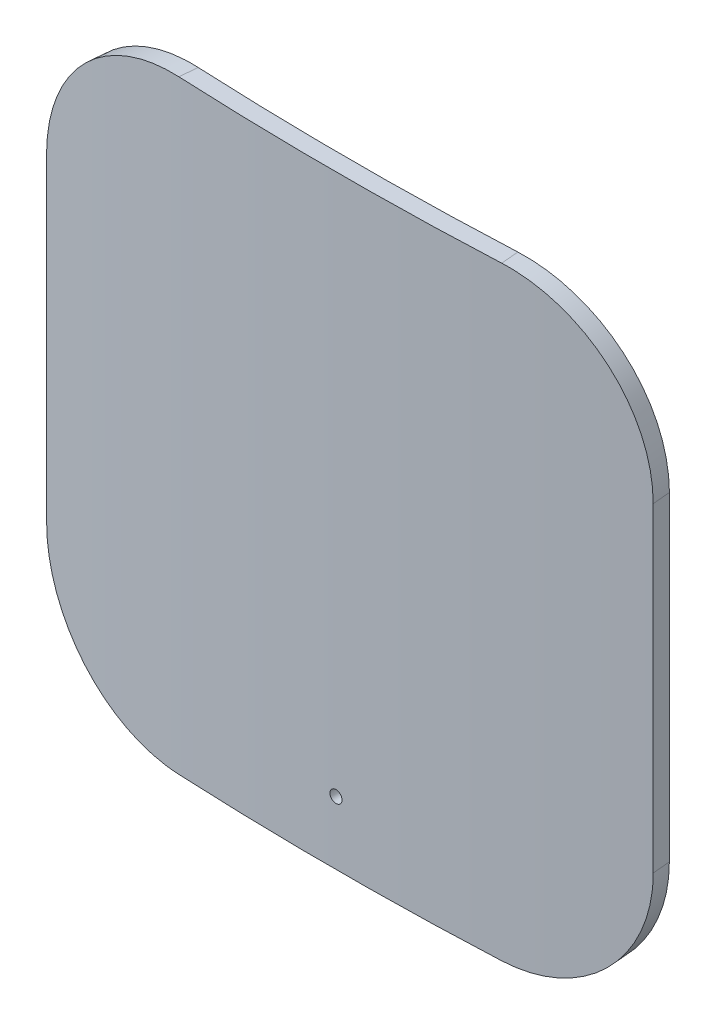
SolidWorks part; units mm, degrees
material "S235JR"
ref_plane "Ebene vorne" through (0, 0, 0) normal (0, 0, 1) x (1, 0, 0)
ref_plane "Ebene oben" through (0, 0, 0) normal (0, 1, 0) x (1, 0, 0)
ref_plane "Ebene rechts" through (0, 0, 0) normal (1, 0, 0) x (0, 0, -1)
sketch "Skizze2" plane through (0, 0, 0) normal (0, 1, 0) x (1, 0, 0)
  line L0 (0, 1909) -> (-169.7777, -2.475) construction
  line L1 (0, 1909) -> (169.7777, -2.475) construction
  line L2 (0, 1909) -> (0, -10) construction
  circle A0 centre (0, 1909) radius 1909 construction
  arc A1 (-169.7777, -2.475) -> (169.7777, -2.475) centre (0, 1909) ccw
  circle A2 centre (0, 1909) radius 1919 construction
extrude "Linear-Austragen-Dünn1" add sketch "Skizze2" along normal blind 170 and the other way blind 170 thin
fillet "Verrundung1" radius 80 4 edges at (-170.2201, -170, 7.4554) (170.2201, -170, 7.4554) (-170.2201, 170, 7.4554) (170.2201, 170, 7.4554)
hole_wizard "Ø6.8 (6.8) Durchmesser Bohrung1" positions "3D-Skizze1" profile "Skizze3" hole size "Ø6.8" standard "DIN" end condition through all
sketch3d "3D-Skizze1"
  point P0 (-0.3045, -134.4199, 20)
  dimension "D1" = 135.9
sketch "Skizze3" plane through (-0.3045, -134.4199, 20) normal (0, 1, 0) x (1, 0, 0.0002)
  line L0 (0, 0) -> (0, 22.0643)
  line L1 (0, 22.0643) -> (3.4, 22.0643)
  line L2 (3.4, 22.0643) -> (3.4, 0)
  line L5 (3.4, 0) -> (0, 0)
  line L11 (0, -6.35) -> (0, 107.95) construction
  dimension "Bohrerdurchmesser" = 6.8
  dimension "Bohrungstiefe" = 22.0643
equation "\"Blechdicke\"= \"Dicke Pflasterblech@Skizze2\""
equation "\"Radius\"= \"D Silo außen@Skizze2\" / 2"
equation "\"Breite\"= \"Breite Pflasterblech@Skizze2\""
equation "\"Höhe\"= \"RD4@Beschriftung\""
